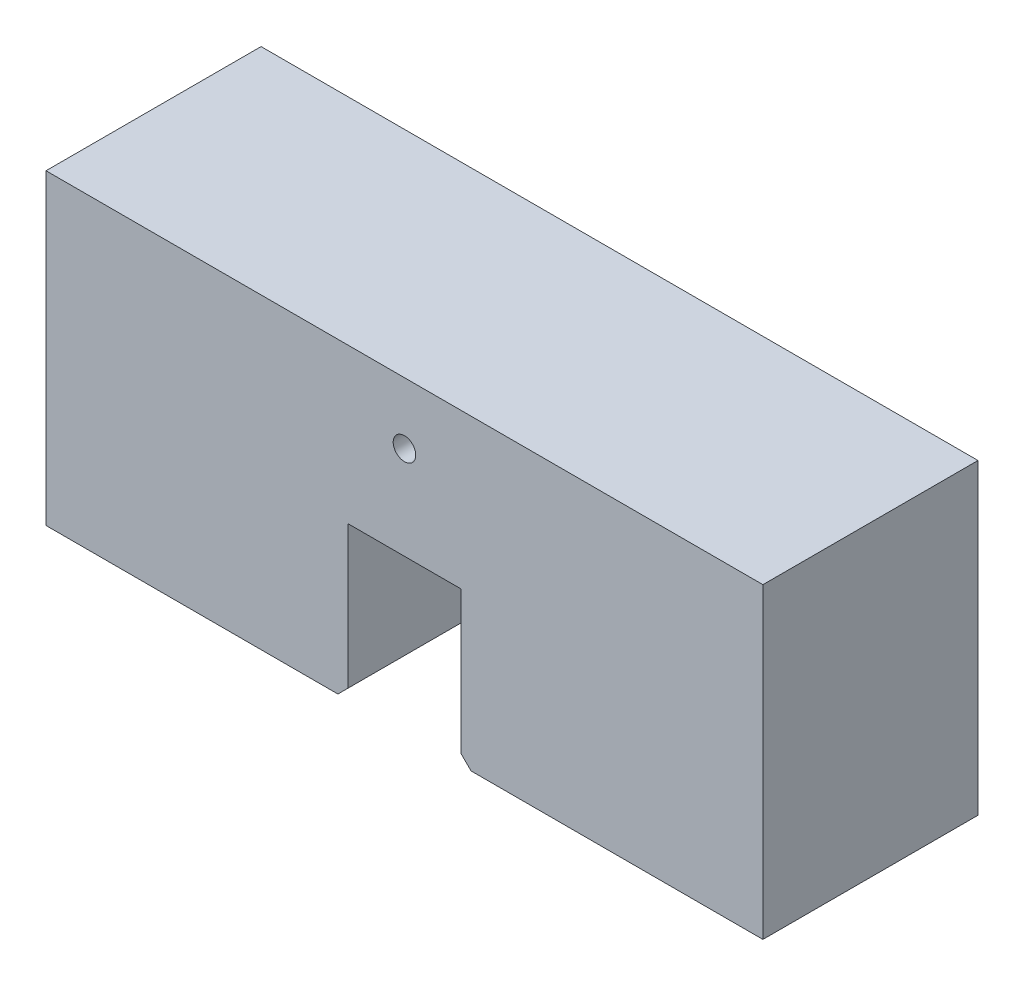
SolidWorks part; units mm, degrees
material "Plain Carbon Steel"
ref_plane "Front Plane" through (0, 0, 0) normal (0, 0, 1) x (1, 0, 0)
ref_plane "Top Plane" through (0, 0, 0) normal (0, 1, 0) x (1, 0, 0)
ref_plane "Right Plane" through (0, 0, 0) normal (1, 0, 0) x (0, 0, -1)
sketch "Sketch1" plane through (0, 0, 0) normal (0, 0, 1) x (1, 0, 0)
  line B0 (350, 232.4214) -> (-350, 232.4214)
  line B1 (-350, 232.4214) -> (-350, -67.5786)
  line B2 (-350, -67.5786) -> (-65, -67.5786)
  line B3 (-65, -67.5786) -> (-55, -57.5786)
  line B4 (-55, 81.4214) -> (55, 81.4214)
  line B5 (-55, -57.5786) -> (-55, 81.4214)
  line B6 (55, -57.5786) -> (55, 81.4214)
  line B7 (65, -67.5786) -> (55, -57.5786)
  line B8 (350, -67.5786) -> (65, -67.5786)
  line B9 (350, 232.4214) -> (350, -67.5786)
sketch_block_instance "Ballast_block-1"
sketch_block "Ballast_block" parameters "D1"=135, "D2"=10, "D3"=230, "D4"=230, "D5"=299, "D6"=285
extrude "Boss-Extrude1" add sketch "Sketch1" along normal mid plane 210
sketch "Sketch2" plane through (0, 0, 0) normal (0, 0, 1) x (1, 0, 0)
  line L0 (0, 0) -> (0, 241.1048) construction
  line L1 (350, 232.4214) -> (-350, 232.4214) construction
  circle A0 centre (0, 172.4214) radius 11
  dimension "D1" = 22
  dimension "D2" = 60
extrude "Cut-Extrude1" cut sketch "Sketch2" against normal through all and the other way through all
